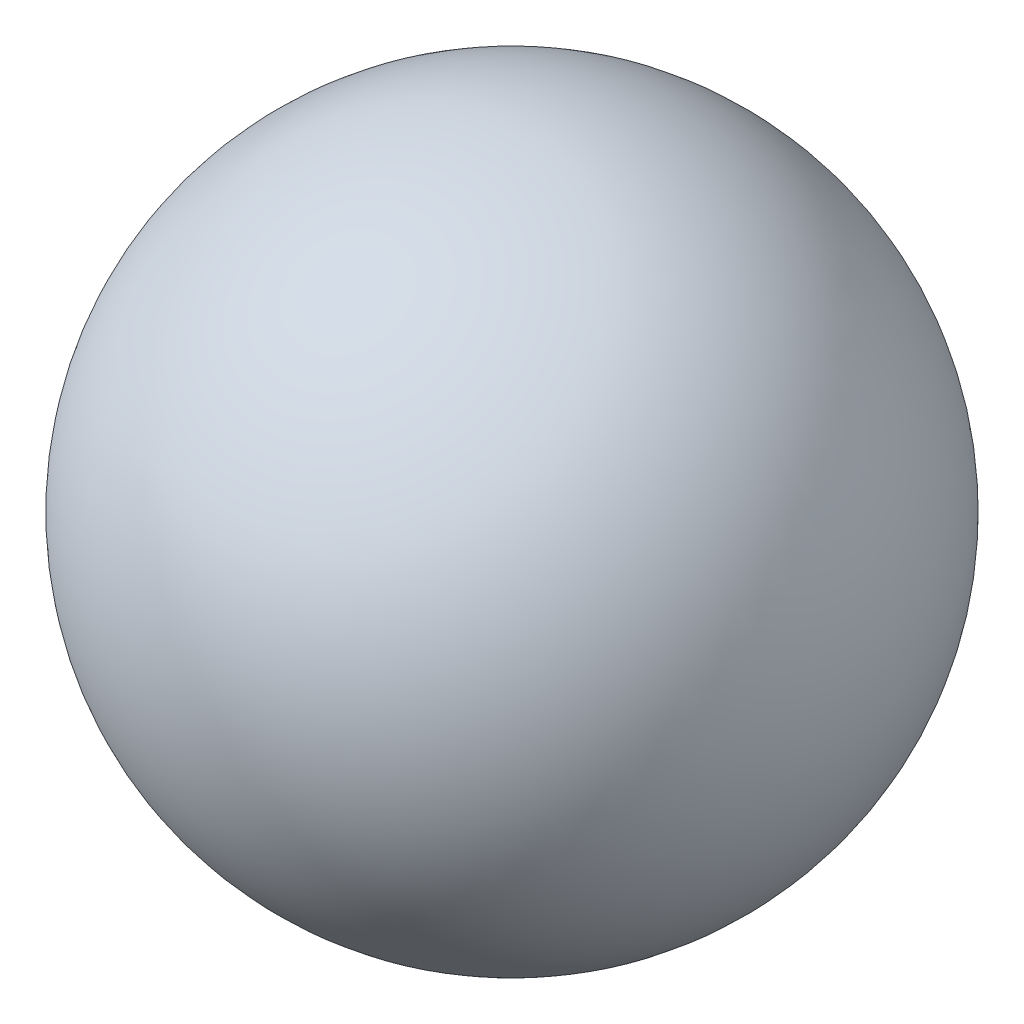
SolidWorks part; units mm, degrees
ref_plane "Front Plane" through (0, 0, 0) normal (0, 0, 1) x (1, 0, 0)
ref_plane "Top Plane" through (0, 0, 0) normal (0, 1, 0) x (1, 0, 0)
ref_plane "Right Plane" through (0, 0, 0) normal (1, 0, 0) x (0, 0, -1)
sketch "Sketch1" plane through (0, 0, 0) normal (0, 0, 1) x (1, 0, 0)
  line L0 (0, 0) -> (0, 64.0599) construction
  line L1 (0, 64.0599) -> (0, -73.0618) construction
  line L2 (0, -1.5) -> (0, 1.5)
  arc A0 (0, -1.5) -> (0, 1.5) centre (0, 0) ccw
revolve "Revolve1" add sketch "Sketch1" angle 360 about L2
